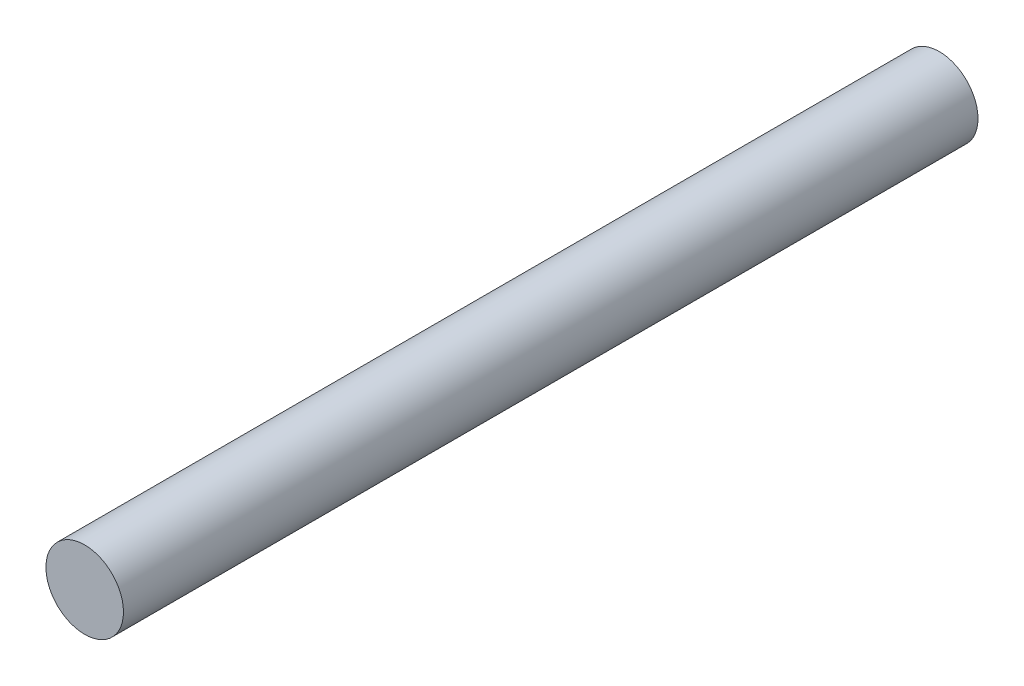
SolidWorks part; units mm, degrees
ref_plane "Ön Düzlem" through (0, 0, 0) normal (0, 0, 1) x (1, 0, 0)
ref_plane "Üst Düzlem" through (0, 0, 0) normal (0, 1, 0) x (1, 0, 0)
ref_plane "Sağ Düzlem" through (0, 0, 0) normal (1, 0, 0) x (0, 0, -1)
sketch "Çizim1" plane through (0, 0, 0) normal (0, 0, 1) x (1, 0, 0)
  circle A0 centre (0, 0) radius 0.5
  dimension "D1" = 1
extrude "Yükseklik-Ekstrüzyon1" add sketch "Çizim1" along normal mid plane 11.02
